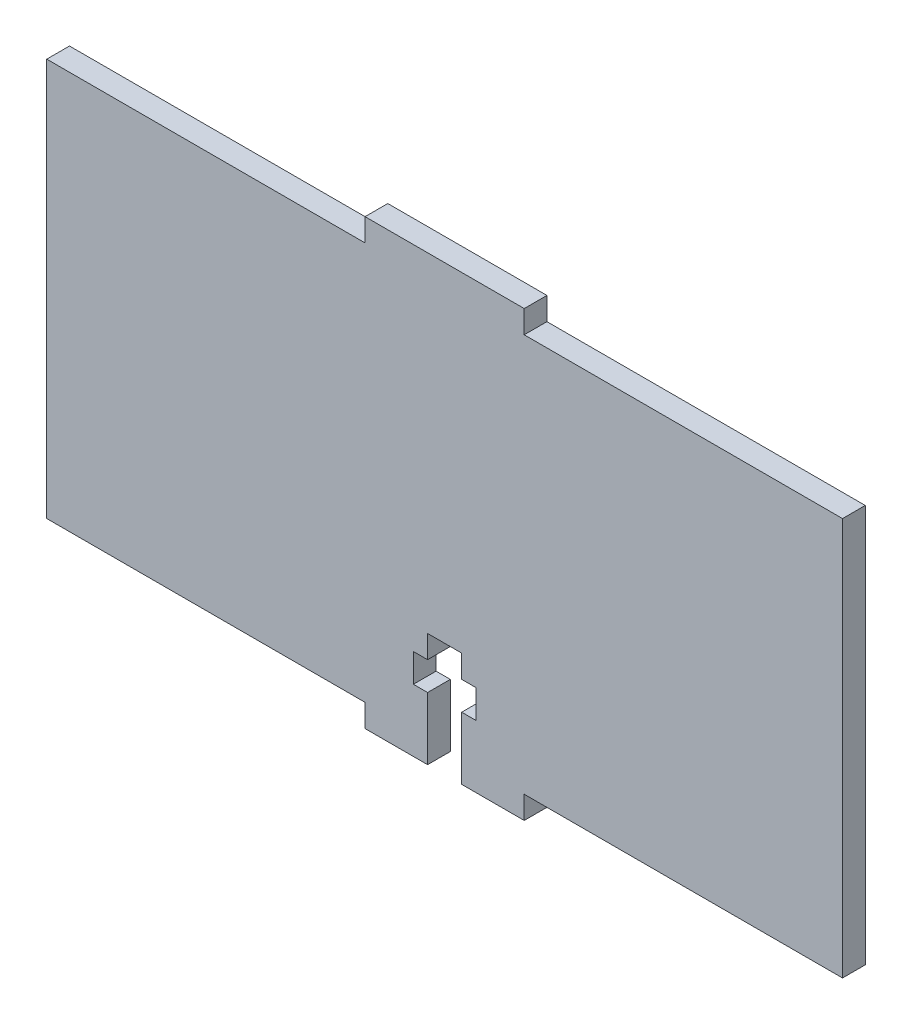
SolidWorks part; units mm, degrees
material "Acrylic (Medium-high impact)"
ref_plane "Front Plane" through (0, 0, 0) normal (0, 0, 1) x (1, 0, 0)
ref_plane "Top Plane" through (0, 0, 0) normal (0, 1, 0) x (1, 0, 0)
ref_plane "Right Plane" through (0, 0, 0) normal (1, 0, 0) x (0, 0, -1)
sketch "Sketch1" plane through (0, 0, 0) normal (0, 0, 1) x (1, 0, 0)
  line L0 (42, 35) -> (70, 35)
  line L1 (0, 0) -> (28, 0)
  line L2 (0, 0) -> (0, 35)
  line L3 (0, 35) -> (28, 35)
  line L4 (70, 0) -> (70, 35)
  line L5 (28, -2) -> (33.5, -2)
  line L6 (28, 0) -> (28, -2)
  line L7 (33.5, -2) -> (33.5, 3.5)
  line L8 (42, 0) -> (42, -2)
  line L9 (42, 0) -> (70, 0)
  line L10 (28, 35) -> (28, 37)
  line L11 (28, 37) -> (42, 37)
  line L12 (42, 35) -> (42, 37)
  line L13 (33.5, 3.5) -> (32.25, 3.5)
  line L14 (32.25, 3.5) -> (32.25, 6)
  line L15 (32.25, 6) -> (33.5, 6)
  line L16 (36.5, 6) -> (36.5, 8)
  line L17 (36.5, 8) -> (33.5, 8)
  line L18 (33.5, 8) -> (33.5, 6)
  line L19 (36.5, 6) -> (37.75, 6)
  line L20 (37.75, 6) -> (37.75, 3.5)
  line L21 (37.75, 3.5) -> (36.5, 3.5)
  line L22 (36.5, 3.5) -> (36.5, -2)
  line L23 (36.5, -2) -> (42, -2)
  line L24 (33.5, -2) -> (36.5, -2) construction
  line L25 (35, -2) -> (35, 8) construction
  dimension "D1" = 2
  dimension "D2" = 70
  dimension "D3" = 35
  dimension "D4" = 14
  dimension "D5" = 28
  dimension "D6" = 3
  dimension "D7" = 2.5
  dimension "D8" = 2
  dimension "D9" = 5.5
  dimension "D10" = 10
extrude "Main Slider Side Down" add sketch "Sketch1" along normal blind 2
